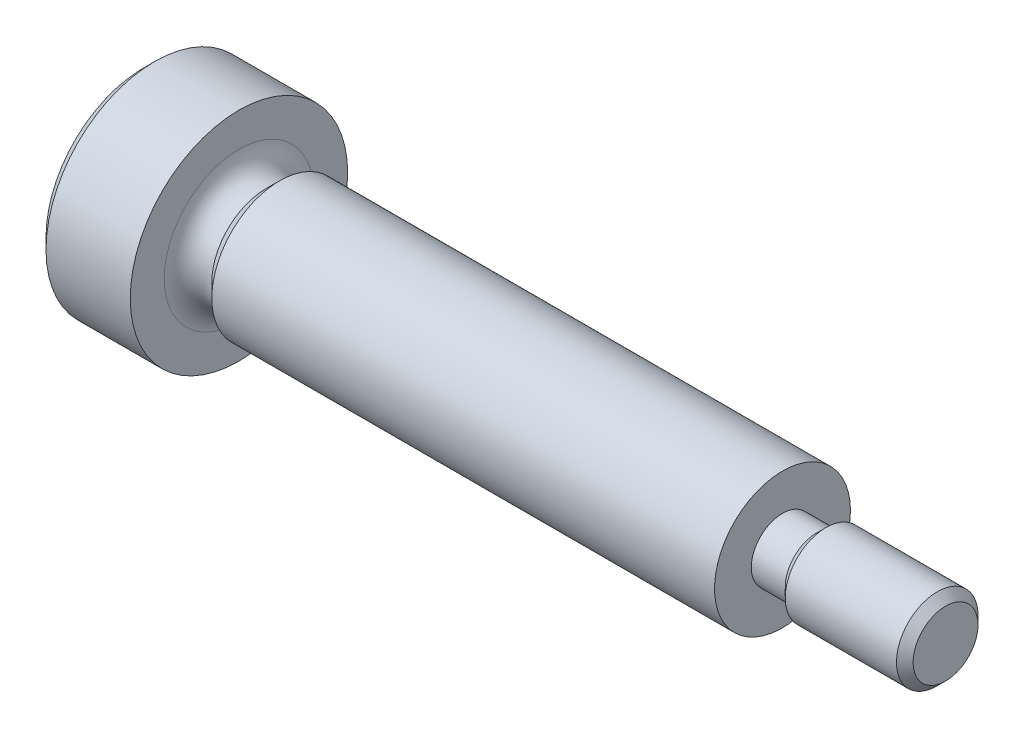
SolidWorks part; units mm, degrees
material "AISI 304"
ref_plane "Front Plane" through (0, 0, 0) normal (0, 0, 1) x (1, 0, 0)
ref_plane "Top Plane" through (0, 0, 0) normal (0, 1, 0) x (1, 0, 0)
ref_plane "Right Plane" through (0, 0, 0) normal (1, 0, 0) x (0, 0, -1)
ref_plane "Plane1" through (0, 0, 0) normal (0, 0, -1) x (-1, 0, 0)
sketch "Sketch1" plane through (0, 0, 0) normal (0, 0, -1) x (-1, 0, 0)
  line L0 (-0.999, 2) -> (-0.999, 0)
  line L1 (-0.999, 0) -> (3.5, 0)
  line L2 (3.5, 0) -> (3.5, 4)
  line L3 (3.5, 4) -> (0, 4)
  line L4 (0, 4) -> (0, 2.75)
  line L5 (-0.999, 0) -> (3.5, 0) construction
  arc A0 (0, 2.75) -> (-0.999, 2) centre (-0.8157, 2.7962) cw
revolve "Revolve1" add sketch "Sketch1" angle 360 about L5
sketch "Sketch2" plane through (0.999, 0, 0) normal (1, 0, 0) x (0, 0, -1)
  circle A0 centre (0, 0) radius 2
extrude "Boss-Extrude1" add sketch "Sketch2" along normal blind 0.5 draft 45 draft outward yes
sketch "Sketch3" plane through (1.499, 0, 0) normal (1, 0, 0) x (0, 0, -1)
  circle A0 centre (0, 0) radius 2.5
extrude "Boss-Extrude2" add sketch "Sketch3" along normal blind 18.501
sketch "Sketch4" plane through (20, 0, 0) normal (1, 0, 0) x (0, 0, -1)
  circle A0 centre (0, 0) radius 1.15
extrude "Boss-Extrude3" add sketch "Sketch4" along normal blind 1.25
sketch "Sketch5" plane through (21.25, 0, 0) normal (1, 0, 0) x (0, 0, -1)
  circle A0 centre (0, 0) radius 1.15
extrude "Boss-Extrude4" add sketch "Sketch5" along normal blind 0.35 draft 45 draft outward yes
sketch "Sketch6" plane through (21.6, 0, 0) normal (1, 0, 0) x (0, 0, -1)
  circle A0 centre (0, 0) radius 1.5
extrude "Boss-Extrude5" add sketch "Sketch6" along normal blind 4.0935
sketch "Sketch7" plane through (25.6935, 0, 0) normal (1, 0, 0) x (0, 0, -1)
  circle A0 centre (0, 0) radius 1.5
extrude "Boss-Extrude6" add sketch "Sketch7" along normal blind 0.3065 draft 45
sketch "Sketch8" plane through (-3.5, 0, 0) normal (-1, 0, 0) x (0, 0, 1)
  line L0 (0, 1.4434) -> (-1.25, 0.7217)
  line L1 (-1.25, 0.7217) -> (-1.25, -0.7217)
  line L2 (-1.25, -0.7217) -> (0, -1.4434)
  line L3 (0, -1.4434) -> (1.25, -0.7217)
  line L4 (1.25, -0.7217) -> (1.25, 0.7217)
  line L5 (1.25, 0.7217) -> (0, 1.4434)
extrude "Cut-Extrude1" cut sketch "Sketch8" against normal blind 1.6
sketch "Sketch9" plane through (0, 0, 0) normal (0, 0, 1) x (1, 0, 0)
  line L0 (-1.9, 1.25) -> (-1.9, 0)
  line L1 (-1.9, 0) -> (-1.1783, 0)
  line L2 (-1.1783, 0) -> (-1.9, 1.25)
  line L3 (-1.9, 0) -> (-1.1783, 0) construction
revolve "Cut-Revolve1" cut sketch "Sketch9" angle 360 about L3
chamfer "Chamfer1" distance 0.4 angle 45 1 edges at (-3.5, 0, 4)
